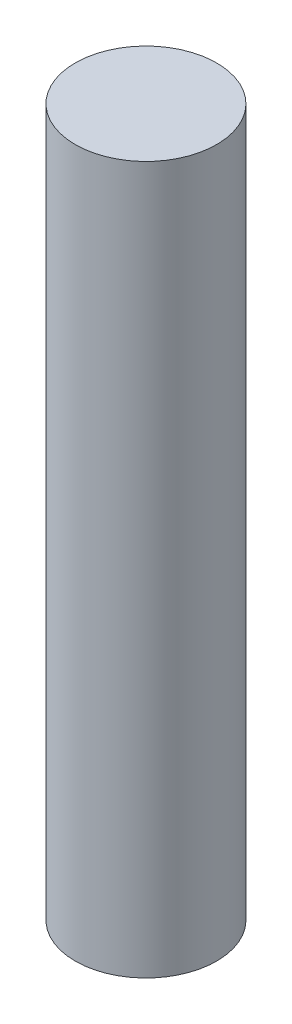
SolidWorks part; units mm, degrees
ref_plane "Front" through (0, 0, 0) normal (0, 0, 1) x (1, 0, 0)
ref_plane "Top" through (0, 0, 0) normal (0, 1, 0) x (1, 0, 0)
ref_plane "Right" through (0, 0, 0) normal (1, 0, 0) x (0, 0, -1)
sketch "Sketch1" plane through (0, 0, 0) normal (0, 1, 0) x (1, 0, 0)
  circle A0 centre (0, 0) radius 2
  dimension "D1" = 4
extrude "Boss-Extrude1" add sketch "Sketch1" along normal blind 20
